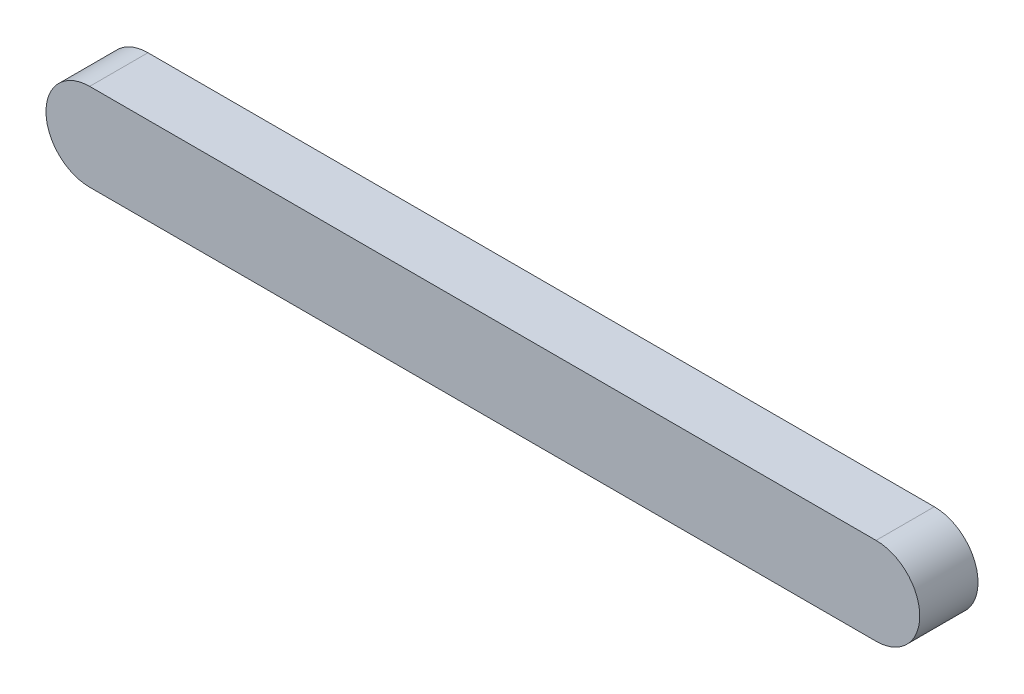
SolidWorks part; units mm, degrees
ref_plane "前视基准面" through (0, 0, 0) normal (0, 0, 1) x (1, 0, 0)
ref_plane "上视基准面" through (0, 0, 0) normal (0, 1, 0) x (1, 0, 0)
ref_plane "右视基准面" through (0, 0, 0) normal (1, 0, 0) x (0, 0, -1)
sketch "草图1" plane through (0, 0, 0) normal (0, 0, 1) x (1, 0, 0)
  line L0 (0, 0) -> (-135, 0) construction
  line L1 (0, -7.5) -> (-135, -7.5)
  line L2 (0, 7.5) -> (-135, 7.5)
  arc A0 (0, -7.5) -> (0, 7.5) centre (0, 0) ccw
  arc A1 (-135, 7.5) -> (-135, -7.5) centre (-135, 0) ccw
  point P2 (-67.5, 0)
  dimension "D1" = 135
  dimension "D2" = 15
extrude "凸台-拉伸1" add sketch "草图1" along normal blind 10
